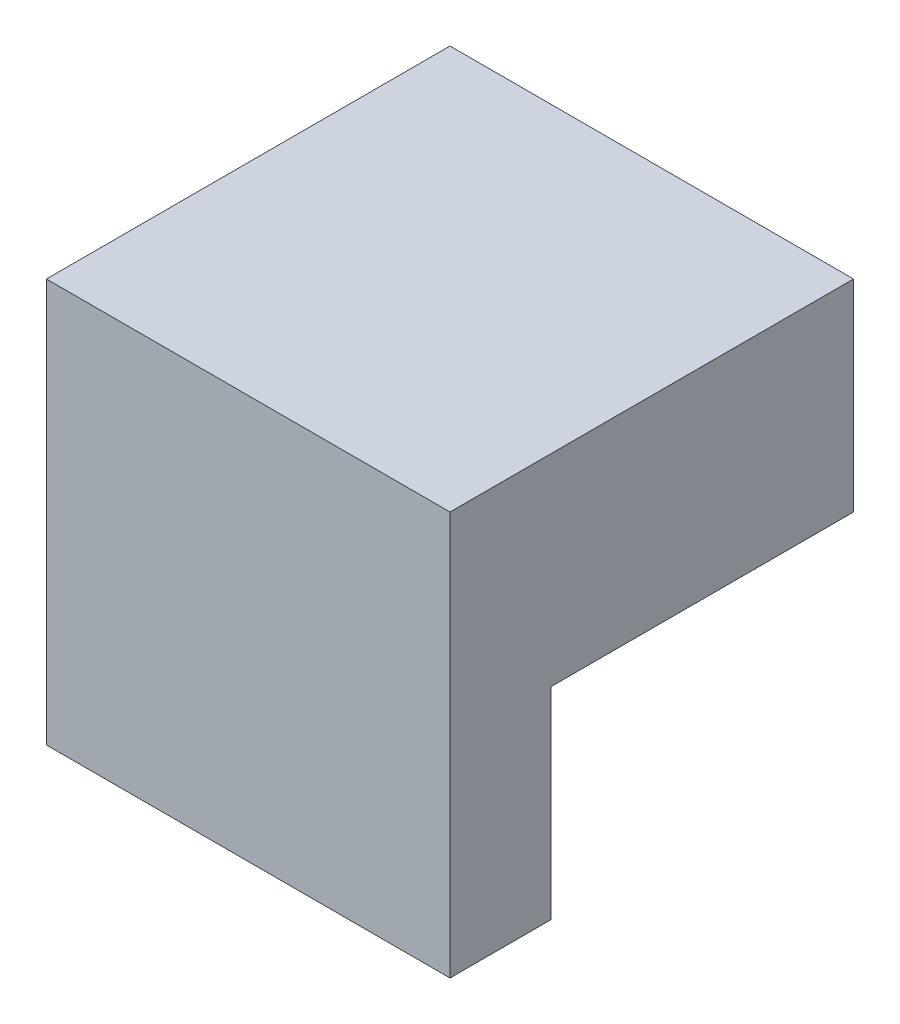
SolidWorks part; units mm, degrees
ref_plane "Front Plane" through (0, 0, 0) normal (0, 0, 1) x (1, 0, 0)
ref_plane "Top Plane" through (0, 0, 0) normal (0, 1, 0) x (1, 0, 0)
ref_plane "Right Plane" through (0, 0, 0) normal (1, 0, 0) x (0, 0, -1)
sketch "Sketch1" plane through (0, 0, 0) normal (0, 0, 1) x (1, 0, 0)
  line L1 (0, 0) -> (40, 0)
  line L2 (0, 0) -> (0, 40)
  line L3 (0, 40) -> (40, 40)
  line L4 (40, 0) -> (40, 40)
  dimension "D1" = 40
  dimension "D2" = 40
extrude "Boss-Extrude1" add sketch "Sketch1" along normal blind 40
sketch "Sketch2" plane through (0, 0, 0) normal (-1, 0, 0) x (0, 0, 1)
  line L1 (0, 0) -> (10, 0)
  line L2 (0, 0) -> (0, 20)
  line L3 (0, 20) -> (10, 20)
  line L4 (10, 0) -> (10, 20)
  dimension "D1" = 10
  dimension "D2" = 20
extrude "Cut-Extrude1" cut sketch "Sketch2" against normal blind 40
sketch "Sketch3" plane through (0, 0, 0) normal (0, -1, 0) x (1, 0, 0)
  line L0 (0, 10) -> (0, 0)
  line L1 (0, 40) -> (0, 10) construction
  line L2 (0, 10) -> (40, 30)
  line L3 (40, 40) -> (40, 10) construction
  line L4 (40, 30) -> (40, 0)
  line L5 (40, 0) -> (0, 0)
  dimension "D1" = 10
  dimension "D2" = 30
extrude "Cut-Extrude2" cut sketch "Sketch3" against normal blind 20
